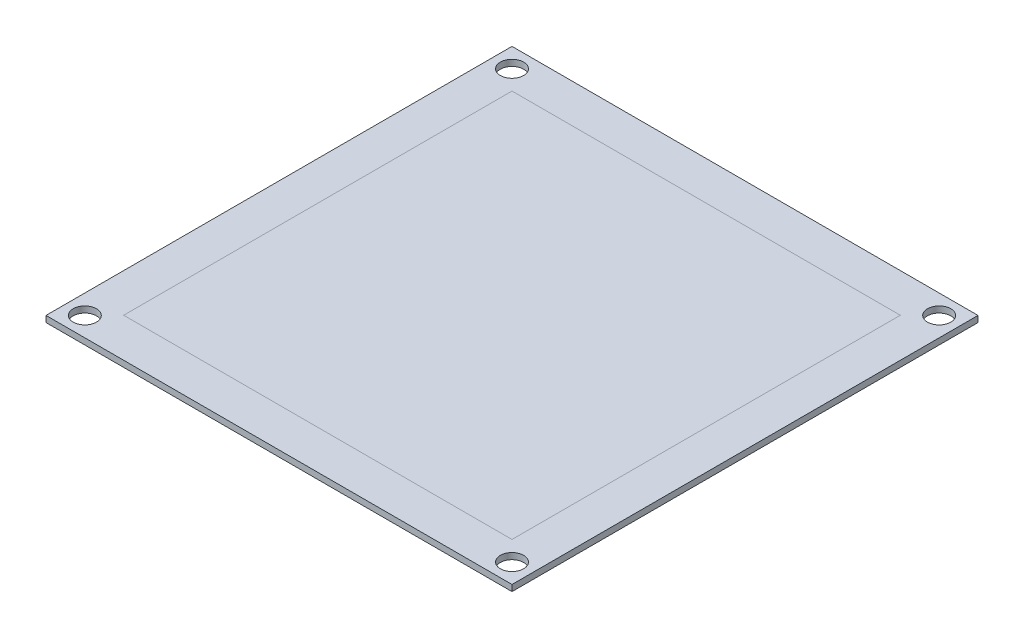
SolidWorks part; units mm, degrees
ref_plane "Front Plane" through (0, 0, 0) normal (0, 0, 1) x (1, 0, 0)
ref_plane "Top Plane" through (0, 0, 0) normal (0, 1, 0) x (1, 0, 0)
ref_plane "Right Plane" through (0, 0, 0) normal (1, 0, 0) x (0, 0, -1)
sketch "Sketch1" plane through (0, 0, 0) normal (0, 1, 0) x (1, 0, 0)
  line L1 (-30, 30) -> (30, 30)
  line L2 (-30, 30) -> (-30, -30)
  line L3 (-30, -30) -> (30, -30)
  line L4 (30, 30) -> (30, -30)
  line L5 (-30, 30) -> (30, -30) construction
  line L6 (-30, -30) -> (30, 30) construction
  point P0 (0, 0)
  dimension "D1" = 60
extrude "Boss-Extrude1" add sketch "Sketch1" along normal blind 0.8
sketch "Sketch2" plane through (0, 0.8, 0) normal (0, 1, 0) x (1, 0, 0)
  line L1 (-25, 25) -> (25, 25)
  line L2 (-25, 25) -> (-25, -25)
  line L3 (-25, -25) -> (25, -25)
  line L4 (25, 25) -> (25, -25)
  line L5 (-25, 25) -> (25, -25) construction
  line L6 (-25, -25) -> (25, 25) construction
  point P0 (0, 0)
  dimension "D1" = 50
surface "Surface-Plane1" sketch "Sketch2"
move or copy body "Body-Move/Copy1" bodies to move or copy 102 copy no translate (0, 0.018, 0)
hole_wizard "Ø3.0 (3) Diameter Hole1" positions "Sketch3" profile "Sketch4" hole size "Ø3.0" standard "ANSI Metric" end condition through all
sketch "Sketch3" plane through (0, 0.8, 0) normal (0, 1, 0) x (1, 0, 0)
  line L0 (-27.5, 27.5) -> (27.5, 27.5) construction
  line L1 (27.5, 27.5) -> (27.5, -27.5) construction
  line L2 (27.5, -27.5) -> (-27.5, -27.5) construction
  line L3 (-27.5, -27.5) -> (-27.5, 27.5) construction
  line L5 (-27.5, -27.5) -> (27.5, 27.5) construction
  line L7 (-27.5, 27.5) -> (27.5, -27.5) construction
  point P0 (-27.5, 27.5)
  point P2 (27.5, 27.5)
  point P4 (27.5, -27.5)
  point P6 (-27.5, -27.5)
  dimension "D1" = 55
sketch "Sketch4" plane through (-27.5, 0.8, -27.5) normal (1, 0, 0) x (0, 0, 1)
  line L0 (0, 0) -> (0, 0.8)
  line L1 (0, 0.8) -> (1.5, 0.8)
  line L2 (1.5, 0.8) -> (1.5, 0)
  line L5 (1.5, 0) -> (0, 0)
  line L11 (0, -6.35) -> (0, 107.95) construction
  dimension "Thru Hole Dia." = 3
  dimension "Thru Hole Depth" = 0.8
